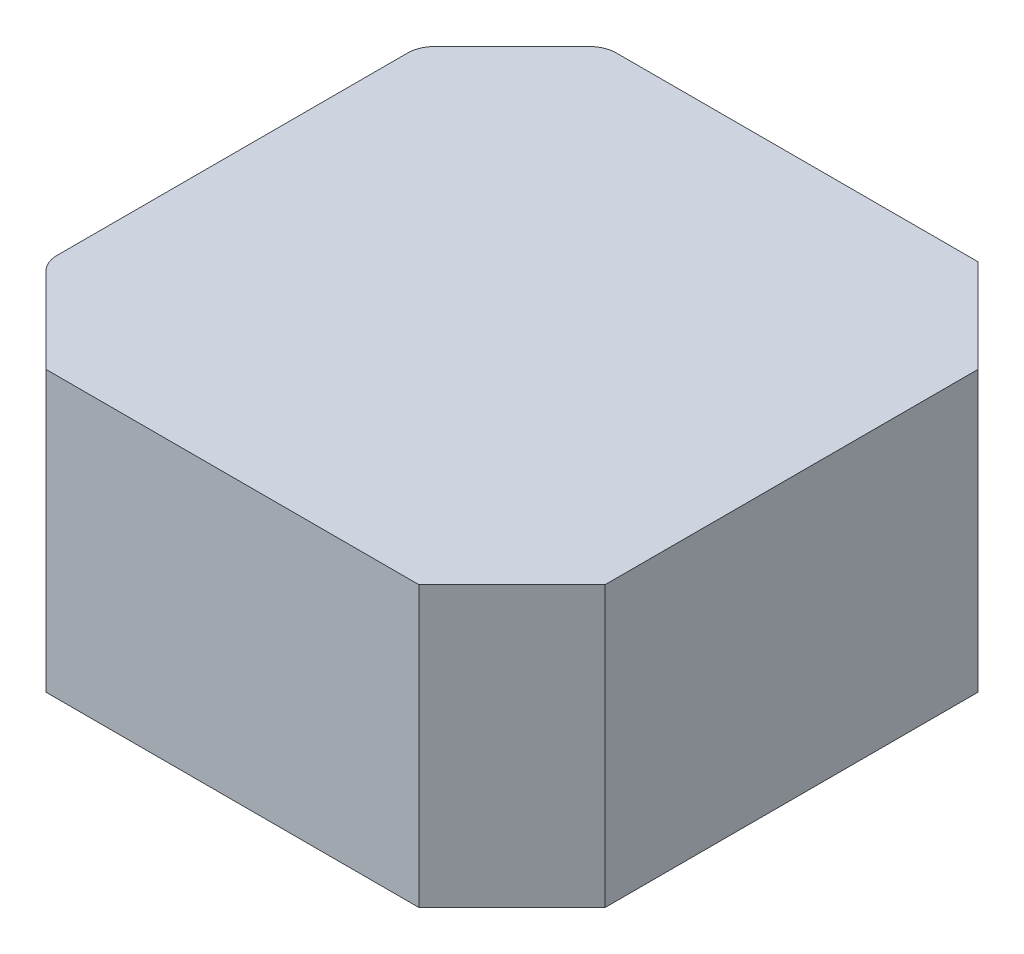
SolidWorks part; units mm, degrees
ref_plane "Front Plane" through (0, 0, 0) normal (0, 0, 1) x (1, 0, 0)
ref_plane "Top Plane" through (0, 0, 0) normal (0, 1, 0) x (1, 0, 0)
ref_plane "Right Plane" through (0, 0, 0) normal (1, 0, 0) x (0, 0, -1)
sketch "Sketch1" plane through (0, 0, 0) normal (0, 1, 0) x (1, 0, 0)
  line L1 (-21, 21) -> (21, 21)
  line L2 (-21, 21) -> (-21, -21)
  line L3 (-21, -21) -> (21, -21)
  line L4 (21, 21) -> (21, -21)
  point P4 (0, 21)
  point P6 (21, 0)
  dimension "D1" = 42
  dimension "D2" = 42
extrude "Boss-Extrude1" add sketch "Sketch1" along normal blind 21
chamfer "Chamfer1" distance 7 angle 45 4 edges at (-21, 10.5, -21) (-21, 10.5, 21) (21, 10.5, 21) (21, 10.5, -21)
fillet "Fillet1" radius 2 3 edges at (-14, 10.5, -21) (-21, 10.5, -14) (-21, 10.5, 14)
